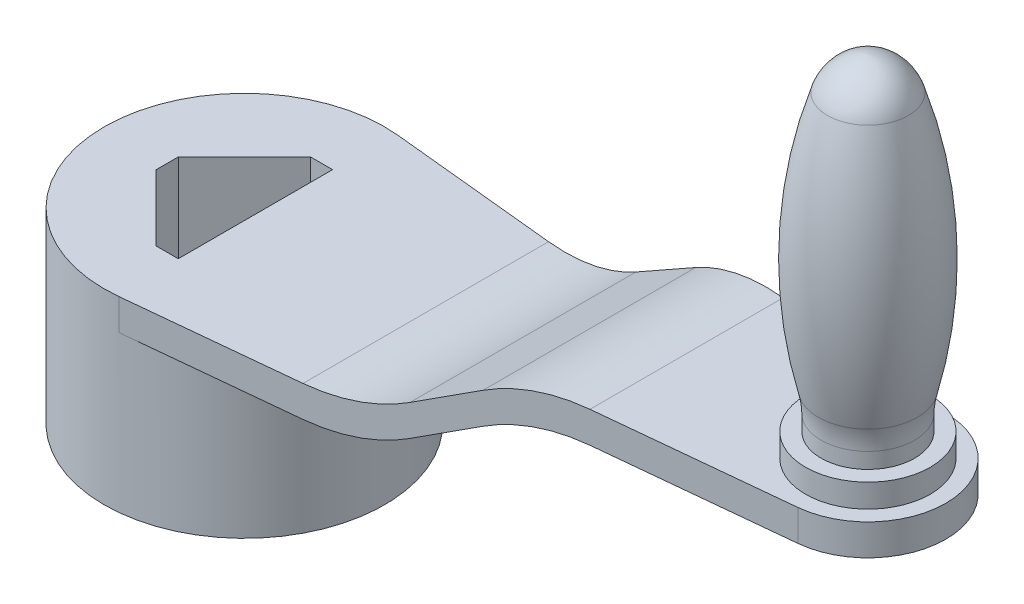
SolidWorks part; units mm, degrees
ref_plane "Ön Düzlem" through (0, 0, 0) normal (0, 0, 1) x (1, 0, 0)
ref_plane "Üst Düzlem" through (0, 0, 0) normal (0, 1, 0) x (1, 0, 0)
ref_plane "Sağ Düzlem" through (0, 0, 0) normal (1, 0, 0) x (0, 0, -1)
sketch "Çizim2" plane through (0, 0, 0) normal (0, 1, 0) x (1, 0, 0)
  circle A0 centre (0, 0) radius 45
  dimension "D1" = 90
extrude "Yükseklik-Ekstrüzyon1" add sketch "Çizim2" along normal mid plane 60
sketch "Çizim3" plane through (0, 30, 0) normal (0, 1, 0) x (1, 0, 0)
  line L0 (0, 0) -> (-24.7487, 0) construction
  line L1 (0, 0) -> (0, 24.7487) construction
  line L2 (-24.7487, 3.5355) -> (-3.5355, 24.7487)
  line L3 (0, 0) -> (24.7487, 0) construction
  line L8 (3.5355, 24.7487) -> (24.7487, 3.5355)
  line L9 (0, 0) -> (0, -24.7487) construction
  line L10 (24.7487, -3.5355) -> (3.5355, -24.7487)
  line L11 (-3.5355, -24.7487) -> (-24.7487, -3.5355)
  line L12 (3.5355, -24.7487) -> (-3.5355, -24.7487)
  line L13 (-24.7487, -3.5355) -> (-24.7487, 3.5355)
  line L14 (-3.5355, 24.7487) -> (3.5355, 24.7487)
  line L15 (24.7487, 3.5355) -> (24.7487, -3.5355)
  line L16 (0, -24.7487) -> (0, -45) construction
  line L17 (3.5355, -24.7487) -> (3.5355, -44.8609) construction
  circle A1 centre (0, 0) radius 45 construction
  circle A2 centre (0, 0) radius 45 construction
  point P4 (-28.2843, 0)
  point P6 (0, 28.2843)
  point P10 (0, -28.2843)
  point P11 (3.5355, -44.8609)
  point P12 (3.5355, -45)
  point P15 (28.2843, 0)
  dimension "D1" = 90
  dimension "D2" = 90
  dimension "D3" = 90
  dimension "D4" = 40
extrude "Kes-Ekstrüzyon1" cut sketch "Çizim3" against normal through all
ref_plane "Düzlem1" through (2.5, 0, 0) normal (1, 0, 0) x (0, 0, -1)
sketch "Çizim4" plane through (0, 0, 0) normal (0, 0, 1) x (1, 0, 0)
  line L0 (0, 30) -> (0, -30) construction
  line L1 (-45, -30) -> (45, -30) construction
  line L2 (3.5355, 30) -> (3.5355, -30) construction
  line L3 (3.5355, 30) -> (3.5355, 20)
  line L4 (3.5355, 30) -> (58.178, 30)
  line L5 (3.5355, 20) -> (58.178, 20)
  line L6 (89.3701, 38.7452) -> (110.6299, 51.6833)
  line L7 (141.822, 60.4285) -> (200, 60.4285)
  line L8 (89.3701, 28.7452) -> (110.6299, 41.6833)
  line L9 (141.822, 50.4285) -> (200, 50.4285)
  line L11 (200, 60.4285) -> (225, 60.4285)
  line L12 (200, 50.4285) -> (225, 50.4285)
  line L13 (225, 50.4285) -> (225, 60.4285)
  line L14 (200, 60.4285) -> (200, 50.4285) construction
  line L15 (212.7602, 60.4285) -> (187.2398, 60.4285) construction
  line L16 (200, 60.4285) -> (200, 50.4285) construction
  arc A0 (141.822, 50.4285) -> (110.6299, 41.6833) centre (141.822, -9.5715) ccw
  arc A1 (141.822, 60.4285) -> (110.6299, 51.6833) centre (141.822, 0.4285) ccw
  arc A2 (58.178, 30) -> (89.3701, 38.7452) centre (58.178, 90) ccw
  arc A3 (58.178, 20) -> (89.3701, 28.7452) centre (58.178, 80) ccw
  point P21 (125, 60.4285)
  point P24 (75, 30)
  point P32 (200, 60.4285)
  dimension "D3" = 50
  dimension "D4" = 60
  dimension "D6" = 10
  dimension "D8" = 54.6425
  dimension "D1" = 10
  dimension "D2" = 120
  dimension "D5" = 200
  dimension "D7" = 58.178
  dimension "D9" = 25
extrude "Yükseklik-Ekstrüzyon2" add sketch "Çizim4" along normal mid plane 90
sketch "Çizim7" plane through (0, 60.4285, 0) normal (0, 1, 0) x (1, 0, 0)
  line L1 (4.5, -44.7744) -> (202.5, -24.8747)
  line L2 (4.5, 44.7744) -> (202.5, 24.8747)
  line L3 (58.178, -45) -> (3.5355, -45) construction
  line L4 (58.178, -45) -> (89.3701, -45) construction
  line L5 (110.6299, -45) -> (89.3701, -45) construction
  line L6 (110.6299, -45) -> (141.822, -45) construction
  line L7 (225, -45) -> (141.822, -45) construction
  line L8 (225, -45) -> (225, 45) construction
  line L9 (225, 45) -> (141.822, 45) construction
  line L10 (141.822, 45) -> (110.6299, 45) construction
  line L11 (110.6299, 45) -> (89.3701, 45) construction
  line L12 (89.3701, 45) -> (58.178, 45) construction
  line L13 (58.178, 45) -> (3.5355, 45) construction
  line L14 (58.178, -45) -> (3.5355, -45)
  line L15 (58.178, -45) -> (89.3701, -45)
  line L16 (110.6299, -45) -> (89.3701, -45)
  line L17 (110.6299, -45) -> (141.822, -45)
  line L18 (225, -45) -> (141.822, -45)
  line L19 (225, -45) -> (225, 45)
  line L20 (225, 45) -> (141.822, 45)
  line L21 (141.822, 45) -> (110.6299, 45)
  line L22 (110.6299, 45) -> (89.3701, 45)
  line L23 (89.3701, 45) -> (58.178, 45)
  line L24 (58.178, 45) -> (3.5355, 45)
  circle A0 centre (200, 0) radius 25
  circle A1 centre (0, 0) radius 45 construction
  circle A2 centre (0, 0) radius 45
  dimension "D1" = 50
ref_plane "Düzlem2" through (0, 60, 0) normal (0, 1, 0) x (1, 0, 0)
sketch "Çizim8" plane through (0, 60, 0) normal (0, 1, 0) x (1, 0, 0)
  line L16 (4.5, 44.7744) -> (202.5, 24.8747)
  line L29 (4.5, -44.7744) -> (202.5, -24.8747)
  line L30 (225, 45) -> (3.5355, 45)
  line L31 (225, 45) -> (225, 0)
  line L32 (225, -45) -> (3.5355, -45)
  line L33 (3.5355, -45) -> (3.5355, -44.8609)
  line L34 (3.5355, 45) -> (3.5355, 44.8609)
  line L35 (225, -45) -> (225, 0)
  circle A0 centre (200, 0) radius 25 construction
  circle A1 centre (0, 0) radius 45 construction
  circle A2 centre (200, 0) radius 25
  circle A3 centre (0, 0) radius 45
extrude "Kes-Ekstrüzyon2" cut sketch "Çizim8" against normal through all contours A3 L16 A2 L31 L30 L34 | A3 L33 L32 L35 A2 L29
sketch "Çizim9" plane through (0, 60, 0) normal (0, 1, 0) x (1, 0, 0)
  line L0 (134.6639, -31.6925) -> (134.6639, -45)
  line L1 (134.6639, -45) -> (225, -45)
  line L2 (225, -45) -> (225, 45)
  line L5 (134.6639, 31.6925) -> (134.6639, 45)
  line L6 (134.6639, 45) -> (225, 45)
  line L7 (134.6639, -31.6925) -> (202.5, -24.8747)
  line L8 (134.6639, 31.6925) -> (202.5, 24.8747)
  circle A0 centre (200, 0) radius 25
  point P7 (0, 0)
  dimension "D1" = 50
extrude "Kes-Ekstrüzyon4" cut sketch "Çizim9" along normal through all contours A0 L2 L6 L5 L8 | A0 L7 L0 L1 L2
sketch "Çizim10" plane through (0, 60.4285, 0) normal (0, 1, 0) x (1, 0, 0)
  circle A0 centre (200, 0) radius 20
  dimension "D1" = 40
extrude "Yükseklik-Ekstrüzyon3" add sketch "Çizim10" along normal blind 7.5
sketch "Çizim12" plane through (0, 0, 0) normal (0, 0, 1) x (1, 0, 0)
  line L0 (185, 67.9285) -> (185, 72.9285)
  line L1 (220, 67.9285) -> (180, 67.9285) construction
  line L2 (200, 67.9285) -> (200, 172.4285)
  line L3 (200, 67.9285) -> (200, 172.4285) construction
  line L5 (185, 67.9285) -> (200, 67.9285)
  arc A0 (185, 72.9285) -> (184.1723, 79.686) centre (157, 72.9285) ccw
  arc A1 (184.1723, 79.686) -> (187.0373, 162.1077) centre (329.7385, 115.8867) cw
  arc A2 (187.0373, 162.1077) -> (200, 172.4285) centre (201.3075, 157.4856) cw
  point P9 (121.9916, 169.9438)
  point P16 (193.0114, 82.1711)
  point P17 (195.07, 85.5978)
  point P18 (182.9046, 146.6034)
  point P19 (189.1923, 90.4395)
  point P20 (183.0842, 145.4119)
  point P21 (200, 161.5803)
  point P22 (0, 0)
  point P23 (0, 0)
  point P24 (0, 0)
  point P30 (52.4879, 140.3725)
  point P32 (215.8277, 79.686)
  point P33 (212.9627, 162.1077)
  point P34 (212.9627, 162.1077)
  point P35 (212.9627, 162.1077)
  dimension "D6" = 15
  dimension "D7" = 150
  dimension "D9" = 28
  dimension "D8" = 82.4217
  dimension "D1" = 5
  dimension "D2" = 15
  dimension "D3" = 5
  dimension "D5" = 104.5
revolve "Döndür1" add sketch "Çizim12" angle 360 about L3
